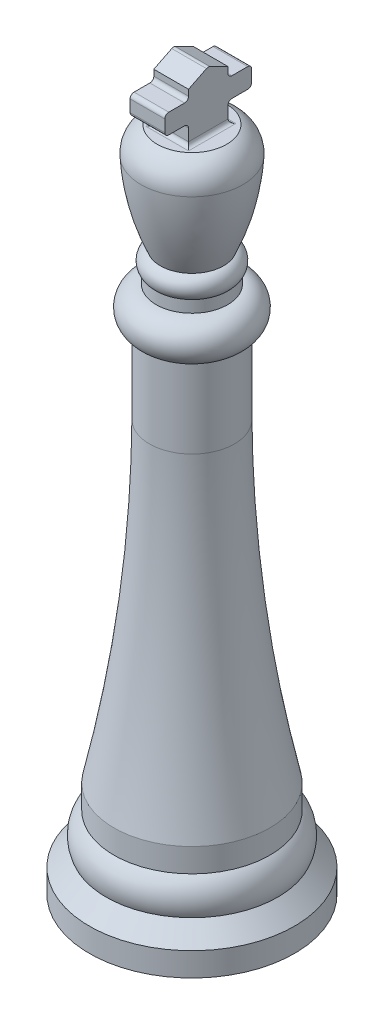
SolidWorks part; units mm, degrees
ref_plane "Front Plane" through (0, 0, 0) normal (0, 0, 1) x (1, 0, 0)
ref_plane "Top Plane" through (0, 0, 0) normal (0, 1, 0) x (1, 0, 0)
ref_plane "Right Plane" through (0, 0, 0) normal (1, 0, 0) x (0, 0, -1)
sketch "Sketch1" plane through (0, 0, 0) normal (0, 0, 1) x (1, 0, 0)
  line L0 (0, 0) -> (6.604, 0)
  line L1 (0, 0) -> (0, 42.926)
  line L2 (6.604, 0) -> (6.604, 1.524)
  line L3 (6.604, 1.524) -> (5.5264, 2.6016)
  line L4 (5.0205, 4.6874) -> (5.0205, 6.2114)
  line L5 (2.7335, 26.472) -> (2.7335, 31.552)
  line L6 (2.3004, 34.0159) -> (2.3004, 34.7779)
  line L8 (2.2343, 42.926) -> (0, 42.926)
  arc A0 (5.5264, 2.6016) -> (5.0205, 4.6874) centre (3.8957, 3.3104) ccw
  arc A1 (2.7335, 31.552) -> (2.3004, 34.0159) centre (2.3004, 32.7459) ccw
  arc A2 (2.3004, 34.7779) -> (2.0374, 36.0544) centre (1.7821, 35.3364) ccw
  arc A3 (3.2797, 41.1965) -> (2.2343, 42.926) centre (1.505, 41.3044) ccw
  spline S0 degree 2 poles (5.0205, 6.2114) (2.7966, 16.192) (2.7335, 26.472) knots 0 0 0 1 1 1
  spline S1 degree 3 poles (2.0374, 36.0544) (2.7546, 37.6906) (3.1715, 39.4171) (3.2797, 41.1965) knots 0 0 0 0 0.825529 0.825529 0.825529 0.825529
  point P18 (0, 0)
  dimension "D6" = 1.778
  dimension "D9" = 1.27
  dimension "D11" = 0.762
  dimension "D12" = 1.778
  dimension "D1" = 6.604
  dimension "D2" = 42.926
  dimension "D3" = 90
  dimension "D4" = 1.524
  dimension "D5" = 1.524
  dimension "D7" = 1.524
  dimension "D8" = 5.08
  dimension "D10" = 0.762
  dimension "D14" = 2.2343
revolve "Revolve1" add sketch "Sketch1" angle 360 about L1
sketch "Sketch3" plane through (0, 42.926, 0) normal (0, 1, 0) x (1, 0, 0)
  line L2 (1.1171, 1.9349) -> (-1.1171, 1.9349)
  line L5 (-1.1171, -1.9349) -> (1.1171, -1.9349)
  line L7 (-1.1171, 1.9349) -> (1.1171, 1.9349)
  line L8 (-1.1171, 1.9349) -> (-1.1171, -1.9349)
  line L9 (-1.1171, -1.9349) -> (1.1171, -1.9349)
  line L10 (1.1171, 1.9349) -> (1.1171, -1.9349)
  line L11 (-1.1171, 1.9349) -> (-2.2343, 0) [skipped]
  line L12 (-2.2343, 0) -> (-1.1171, -1.9349) [skipped]
  line L13 (1.1171, -1.9349) -> (2.2343, 0) [skipped]
  line L14 (2.2343, 0) -> (1.1171, 1.9349) [skipped]
extrude "Boss-Extrude1" add sketch "Sketch3" along normal blind 3.81 contours L10 L2 L8 L5
sketch "Sketch4" plane through (0, 0, -1.9349) normal (0, 0, -1) x (-1, 0, 0)
  line L1 (-1.1171, 46.736) -> (1.1171, 46.736)
  line L2 (-1.1171, 46.736) -> (-1.1171, 42.926)
  line L3 (-1.1171, 42.926) -> (1.1171, 42.926)
  line L4 (1.1171, 46.736) -> (1.1171, 42.926)
extrude "Boss-Extrude2" add sketch "Sketch4" along normal blind 1.27
sketch "Sketch7" plane through (0, 0, 1.9349) normal (0, 0, 1) x (1, 0, 0)
  line L1 (-1.1171, 46.736) -> (1.1171, 46.736)
  line L2 (-1.1171, 46.736) -> (-1.1171, 42.926)
  line L3 (-1.1171, 42.926) -> (1.1171, 42.926)
  line L4 (1.1171, 46.736) -> (1.1171, 42.926)
extrude "Boss-Extrude3" add sketch "Sketch7" along normal blind 1.27
sketch "Sketch11" plane through (1.1171, 0, 0) normal (1, 0, 0) x (0, 0, -1)
  line L0 (-1.3381, 42.926) -> (1.2019, 42.926)
  line L1 (1.9349, 42.926) -> (-1.9349, 42.926) construction
  line L2 (-0.0681, 42.926) -> (-0.0681, 46.736) construction
  line L3 (3.2049, 46.736) -> (-3.2049, 46.736) construction
  line L4 (1.2019, 42.926) -> (1.2019, 43.942)
  line L5 (1.4559, 44.196) -> (2.4719, 44.196)
  line L6 (2.7259, 44.45) -> (2.7259, 45.212)
  line L7 (2.4719, 45.466) -> (1.4559, 45.466)
  line L8 (1.2019, 45.72) -> (1.2019, 46.1062)
  line L9 (1.2019, 46.1062) -> (0.0447, 46.68)
  line L10 (-1.3381, 42.926) -> (-1.3381, 43.942)
  line L11 (-1.5921, 44.196) -> (-2.6081, 44.196)
  line L12 (-2.8621, 44.45) -> (-2.8621, 45.212)
  line L13 (-2.6081, 45.466) -> (-1.5921, 45.466)
  line L14 (-1.3381, 45.72) -> (-1.3381, 46.1062)
  line L15 (-1.3381, 46.1062) -> (-0.181, 46.68)
  arc A0 (-1.3381, 43.942) -> (-1.5921, 44.196) centre (-1.5921, 43.942) ccw
  arc A1 (1.2019, 43.942) -> (1.4559, 44.196) centre (1.4559, 43.942) cw
  arc A2 (2.4719, 44.196) -> (2.7259, 44.45) centre (2.4719, 44.45) ccw
  arc A3 (2.7259, 45.212) -> (2.4719, 45.466) centre (2.4719, 45.212) ccw
  arc A4 (-2.8621, 45.212) -> (-2.6081, 45.466) centre (-2.6081, 45.212) cw
  arc A5 (-2.6081, 44.196) -> (-2.8621, 44.45) centre (-2.6081, 44.45) cw
  arc A6 (0.0447, 46.68) -> (-0.181, 46.68) centre (-0.0681, 46.4525) ccw
  arc A7 (1.4559, 45.466) -> (1.2019, 45.72) centre (1.4559, 45.72) cw
  arc A8 (-1.5921, 45.466) -> (-1.3381, 45.72) centre (-1.5921, 45.72) ccw
  point P5 (-0.0681, 42.926)
  point P21 (-1.3381, 44.196)
  point P24 (1.2019, 44.196)
  point P27 (2.7259, 44.196)
  point P30 (2.7259, 45.466)
  point P33 (-2.8621, 45.466)
  point P36 (-2.8621, 44.196)
  point P42 (1.2019, 45.466)
  point P45 (-1.3381, 45.466)
  line M15 (-3.2049, 42.926) -> (-1.9349, 42.926)
  line M16 (-1.9349, 42.926) -> (1.9349, 42.926)
  line M17 (1.9349, 42.926) -> (3.2049, 42.926)
  line M18 (3.2049, 42.926) -> (3.2049, 46.736)
  line M19 (3.2049, 46.736) -> (-3.2049, 46.736)
  line M20 (-3.2049, 46.736) -> (-3.2049, 42.926)
  dimension "D7" = 0.254
  dimension "D1" = 2.54
  dimension "D2" = 1.27
  dimension "D3" = 1.524
  dimension "D4" = 1.27
  dimension "D5" = 1.524
  dimension "D6" = 0.6402
extrude "Cut-Extrude3" cut sketch "Sketch11" against normal blind 2.286 contours A6 L2 L10 A0 L11 A5 L12 A4 L13 A8 L14 L15 M19 M20 M15 M16 | L2 A6 L9 L8 A7 L7 A3 L6 A2 L5 A1 L4 M16 M17 M18 M19
fillet "Fillet1" radius 0.254 4 edges at (0, 42.926, -1.2019) (1.1171, 42.926, 0.0681) (-1.1171, 42.926, 0.0681) (0, 42.926, 1.3381)
